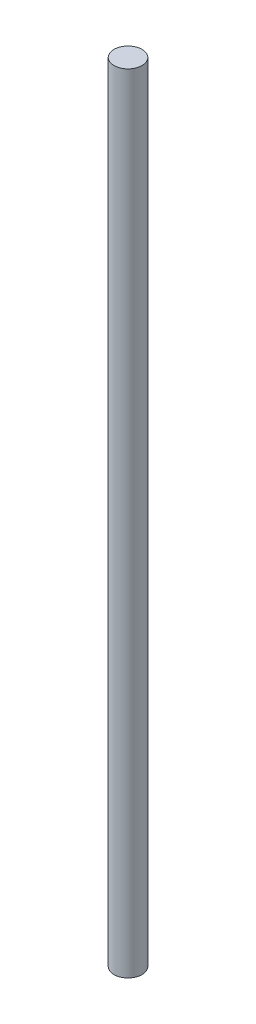
SolidWorks part; units mm, degrees
ref_plane "前视基准面" through (0, 0, 0) normal (0, 0, 1) x (1, 0, 0)
ref_plane "上视基准面" through (0, 0, 0) normal (0, 1, 0) x (1, 0, 0)
ref_plane "右视基准面" through (0, 0, 0) normal (1, 0, 0) x (0, 0, -1)
other "Configuration Table"
sketch "Sketch1" plane through (0, 0, 0) normal (0, 0, 1) x (1, 0, 0)
  line L0 (4.45, 204) -> (0, 204)
  line L1 (0, 204) -> (0, -46)
  line L2 (0, -46) -> (4.45, -46)
  line L3 (4.45, -46) -> (4.45, 204)
  line L4 (0, 204) -> (0, -46) construction
  dimension "D1" = 4.45
  dimension "D2" = 250
  dimension "D3" = 204
revolve "Revolve1" add sketch "Sketch1" angle 360 about L4
cosmetic thread "Cosmetic Thread1"
